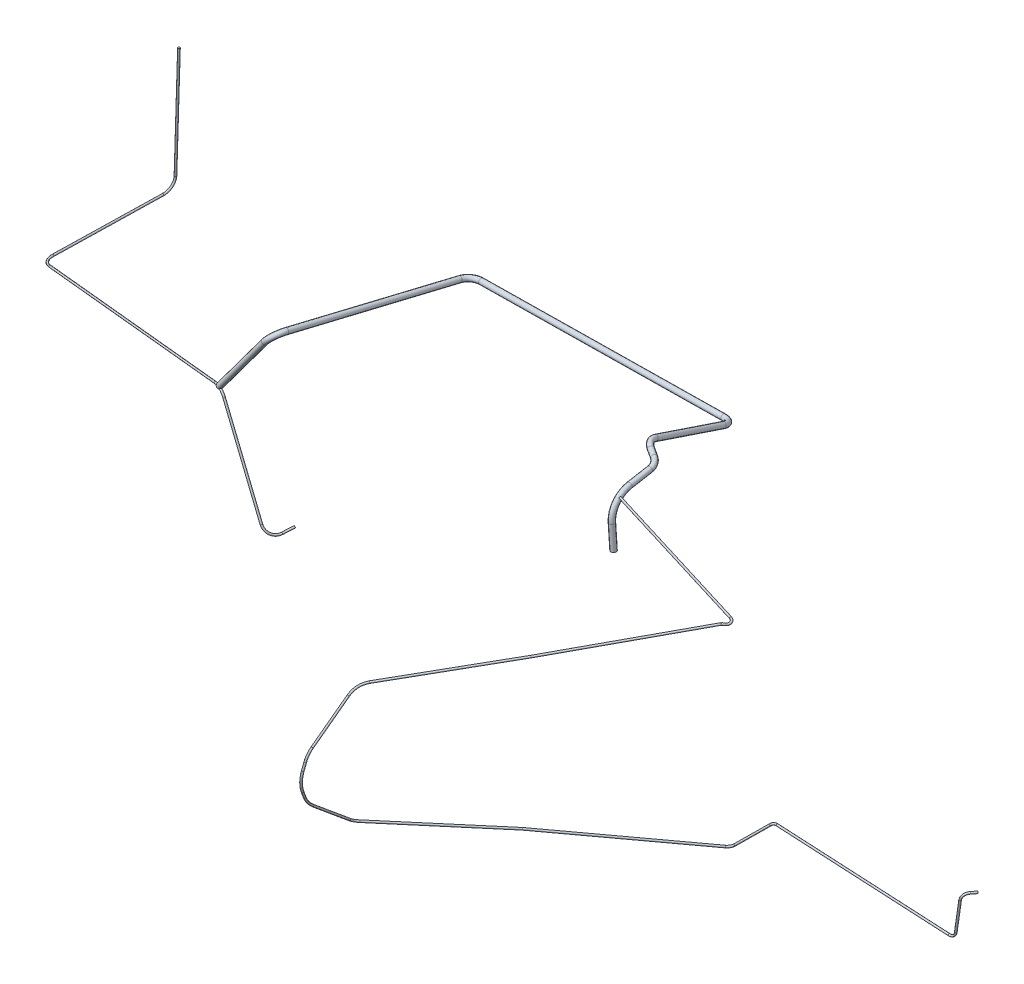
SolidWorks part; units mm, degrees
ref_plane "Front Plane" through (0, 0, 0) normal (0, 0, 1) x (1, 0, 0)
ref_plane "Top Plane" through (0, 0, 0) normal (0, 1, 0) x (1, 0, 0)
ref_plane "Right Plane" through (0, 0, 0) normal (1, 0, 0) x (0, 0, -1)
sketch3d "Szkic 3D1"
  line L0 (118.6334, -241.8152, 530.8128) -> (126.1477, -236.1929, 505.1914)
  line L1 (92.7074, -219.0471, 559.88) -> (-28.1616, -0.6474, 537.4445)
  line L2 (-58.5393, 14.2321, 530.3794) -> (-646.2538, -88.7961, 379.7568)
  line L3 (-668.6435, -91.6493, 348.0488) -> (-647.2132, -76.58, 79.4296)
  line L4 (-642.2695, -45.2392, 51.4403) -> (-614.8845, 270.4014, 69.5762)
  arc A0 (-642.2695, -45.2392, 51.4403) -> (-647.2132, -76.58, 79.4296) centre (-644.6374, -46.7499, 81.3085) ccw
  arc A1 (-668.6435, -91.6493, 348.0488) -> (-646.2538, -88.7961, 379.7568) centre (-639.2442, -86.2938, 350.6947) ccw
  arc A2 (-28.1616, -0.6474, 537.4445) -> (-58.5393, 14.2321, 530.3794) centre (-53.4158, -15.3263, 530.6067) ccw
  arc A3 (92.7074, -219.0471, 559.88) -> (118.6334, -241.8152, 530.8128) centre (102.9496, -216.2612, 531.8205) ccw
  spline S0 degree 3 poles (-43.8939, 18.1609, 559.9156) (-56.5359, -9.6744, 555.7329) (-50.4168, -8.8135, 531.5086) (-37.7748, 19.0219, 535.6913) knots 0 0 0 0 1 1 1 1 weights 1 0.333333 0.333333 1 construction
  point P0 (-614.8845, 270.4014, 69.5762)
  point P1 (-644.8442, -74.9142, 49.7352)
  point P3 (-670.6739, -93.077, 373.4983)
  point P5 (-38.3547, 17.7705, 535.5525)
  point P7 (109.21, -248.8658, 562.9432)
  point P10 (126.1477, -236.1929, 505.1914)
  point P19 (-644.8442, -74.9142, 49.7352)
  point P20 (-674.4316, -44.0371, 79.0837)
  point P23 (-670.6739, -93.077, 373.4983)
  point P24 (-644.7222, -56.8233, 351.911)
  point P27 (-38.3547, 17.7705, 535.5525)
  point P28 (-60.6885, -16.3632, 559.6933)
  point P31 (109.21, -248.8658, 562.9432)
  point P32 (127.1522, -201.8118, 542.0895)
  dimension "D1" = 30
  dimension "D2" = 30
  dimension "D3" = 30
  dimension "D4" = 30
sweep "Wyciągnięcie po ścieżce1" add path "Szkic 3D1" circular profile diameter 5 parameters "D3"=5
sketch3d "Szkic 3D3"
  line L0 (989.8027, 219.1816, 531.8369) -> (993.064, 156.0841, 530.7633)
  line L1 (987.1848, 269.8281, 532.6986) -> (993.064, 156.0841, 530.7633) construction
  line L2 (987.6129, 279.1527, 482.8435) -> (988.0685, 289.0787, 429.7731)
  line L3 (973.366, 297.4051, 404.5748) -> (955.7907, 303.4336, 395.2068)
  line L4 (938.0833, 303.0691, 365.1368) -> (941.6159, 246.4526, 189.4723)
  line L5 (913.4119, 235.9721, 160.7825) -> (245.1625, 197.8978, 131.614)
  line L6 (213.9993, 199.7803, 157.18) -> (154.871, 250.8882, 555.5945)
  line L7 (127.0667, 227.5957, 584.4501) -> (-45.7126, 13.3559, 531.0103)
  arc A0 (154.871, 250.8882, 555.5945) -> (127.0667, 227.5957, 584.4501) centre (135.1657, 228.2674, 555.5718) ccw
  arc A1 (245.1625, 197.8978, 131.614) -> (213.9993, 199.7803, 157.18) centre (243.6407, 201.8549, 161.3129) ccw
  arc A2 (941.6159, 246.4526, 189.4723) -> (913.4119, 235.9721, 160.7825) centre (911.6463, 245.1126, 189.3015) ccw
  arc A3 (938.0833, 303.0691, 365.1368) -> (955.7907, 303.4336, 395.2068) centre (965.0571, 290.7396, 369.653) ccw
  arc A4 (973.366, 297.4051, 404.5748) -> (988.0685, 289.0787, 429.7731) centre (958.8847, 295.9515, 430.8079) ccw
  arc A5 (987.6129, 279.1527, 482.8435) -> (989.8027, 219.1816, 531.8369) centre (990.8388, 220.2557, 471.8555) ccw
  point P0 (-45.7126, 13.3559, 531.0103)
  point P1 (149.5563, 255.482, 591.406)
  point P2 (217.9696, 196.3485, 130.427)
  point P3 (942.1676, 237.6104, 162.0377)
  point P4 (937.6728, 309.6481, 385.5497)
  point P5 (988.2169, 292.3112, 412.4905)
  point P6 (993.064, 156.0841, 530.7633)
  point P17 (149.5563, 255.482, 591.406)
  point P18 (157.3606, 208.9273, 561.3466)
  point P21 (217.9696, 196.3485, 130.427)
  point P22 (242.1252, 231.5438, 157.2795)
  point P25 (942.1676, 237.6104, 162.0377)
  point P26 (910.4235, 273.6353, 180.0841)
  point P29 (937.6728, 309.6481, 385.5497)
  point P30 (978.1752, 316.4947, 361.616)
  point P33 (988.2169, 292.3112, 412.4905)
  point P34 (951.9391, 267.2749, 425.3848)
  point P37 (987.1848, 269.8281, 532.6986)
  point P39 (1050.7499, 223.3339, 472.9456)
  point P40 (1025.4433, 280.7615, 422.3662)
  point P41 (0, 0, 0)
  point P42 (0, 0, 0)
  point P43 (1017.6285, 227.4395, 548.7936)
  point P44 (0, 0, 0)
  point P45 (996.948, 289.329, 478.9412)
  point P46 (996.9218, 289.3378, 480.9302)
  point P47 (0, 0, 0)
  point P48 (985.8788, 155.3262, 554.8039)
  point P49 (990.8026, 156.0347, 535.038)
  point P50 (0, 0, 0)
  point P51 (997.2337, 289.2337, 481.4121)
  point P52 (0, 0, 0)
  point P53 (996.4685, 282.7751, 481.4194)
  point P54 (991.2305, 283.0725, 481.6954)
  point P55 (987.6129, 279.1527, 482.8435)
  point P56 (0, 0, 0)
  point P57 (993.064, 156.0841, 530.7633)
  dimension "D1" = 30
  dimension "D2" = 30
  dimension "D3" = 30
  dimension "D4" = 30
  dimension "D5" = 30
  dimension "D6" = 60
sweep "Wyciągnięcie po ścieżce6" add path "Szkic 3D3" circular profile diameter 14 parameters "D3"=14
sketch3d "Szkic 3D5"
  line L5 (1297.1378, 181.2424, 546.2056) -> (993.3621, 268.815, 513.8045)
  point P0 (993.3621, 268.815, 513.8045)
  point P1 (0, 0, 0)
  point P2 (0, 0, 0)
  point P3 (0, 0, 0)
  point P4 (1297.1378, 181.2424, 546.2056)
sweep "Wyciągnięcie po ścieżce8" add path "Szkic 3D5" circular profile diameter 5 parameters "D3"=5
sketch3d "Szkic 3D7"
  line L0 (1317.9997, 171.2228, 571.7296) -> (1089.6413, 119.1433, 845.116)
  line L1 (1089.6413, 119.1433, 845.116) -> (892.0087, 75.9961, 1072.9769)
  line L2 (873.0448, 54.6235, 1110.3704) -> (862.0854, -27.3683, 1194.7376)
  line L3 (859.4121, -54.1309, 1210.6137) -> (858.0564, -72.0891, 1215.615)
  line L4 (854.0483, -123.8873, 1212.4709) -> (852.7489, -140.2636, 1205.6842)
  line L5 (851.4146, -171.5957, 1182.5394) -> (852.2453, -250.6918, 1087.0711)
  line L6 (859.9208, -260.558, 1067.5275) -> (1046.5433, -305.8392, 825.1721)
  arc A0 (873.0448, 54.6235, 1110.3704) -> (892.0087, 75.9961, 1072.9769) centre (921.6424, 26.4429, 1089.2961) ccw
  arc A1 (859.4121, -54.1309, 1210.6137) -> (862.0854, -27.3683, 1194.7376) centre (862.9992, -70.4504, 1152.9872) ccw
  arc A2 (854.0483, -123.8873, 1212.4709) -> (858.0564, -72.0891, 1215.615) centre (855.986, -93.3997, 1138.5334) ccw
  arc A3 (851.4146, -171.5957, 1182.5394) -> (852.7489, -140.2636, 1205.6842) centre (864.7911, -110.8021, 1132.288) ccw
  arc A4 (859.9208, -260.558, 1067.5275) -> (852.2453, -250.6918, 1087.0711) centre (877.4361, -238.0392, 1076.8075) ccw
  point P1 (875.4174, 72.3739, 1092.1058)
  point P2 (860.5852, -38.5915, 1206.286)
  point P3 (856.0602, -98.5312, 1222.979)
  point P4 (851.28, -158.7766, 1198.012)
  point P5 (852.3296, -258.7161, 1077.3857)
  point P6 (1046.5433, -305.8392, 825.1721)
  point P7 (1089.6413, 119.1433, 845.116)
  point P8 (1317.9997, 171.2228, 571.7296)
  point P9 (1317.9997, 171.2228, 571.7296)
  point P10 (1089.6413, 119.1433, 845.116)
  point P11 (1317.9997, 171.2228, 571.7296)
  point P20 (1344.5343, 169.194, 550.9786)
  point P22 (875.4174, 72.3739, 1092.1058)
  point P23 (886.8962, -6.3029, 1052.9587)
  point P26 (860.5852, -38.5915, 1206.286)
  point P27 (803.2649, -67.2304, 1148.357)
  point P30 (856.0602, -98.5312, 1222.979)
  point P31 (776.2236, -87.2547, 1138.9768)
  point P34 (851.28, -158.7766, 1198.012)
  point P35 (785.9191, -100.8386, 1123.3468)
  point P38 (852.3296, -258.7161, 1077.3857)
  point P39 (861.1454, -218.7104, 1060.6517)
  point P40 (1344.8319, 167.7288, 549.6777)
  point P41 (1346.3485, 167.7529, 549.2822)
  point P42 (0, 0, 0)
  point P43 (0, 0, 0)
  point P44 (928.6967, 42.8842, 509.4356)
  point P45 (1026.5062, 427.7046, 632.5039)
  point P46 (0, 0, 0)
  point P47 (1015.5264, 364.4728, 564.5444)
  point P48 (950.6862, 112.5248, 491.4952)
  point P49 (841.9268, -160.1525, 774.184)
  point P50 (1171.444, 37.1322, 483.201)
  point P51 (1233.7113, 209.6921, 505.3444)
  point P52 (0, 0, 0)
  point P53 (1304.541, 240.922, 556.3461)
  point P54 (1299.8089, 183.2482, 535.0836)
  point P55 (1329.2568, 167.4699, 554.1711)
  point P56 (1317.9997, 171.2228, 571.7296)
  dimension "D1" = 60
  dimension "D2" = 60
  dimension "D3" = 80
  dimension "D4" = 80
  dimension "D5" = 30
  dimension "D6" = 360
sweep "Wyciągnięcie po ścieżce9" add path "Szkic 3D7" circular profile diameter 5 parameters "D3"=5
sketch3d "3DSketch3"
  line L0 (1297.1378, 181.2424, 546.2056) -> (1319.4526, 174.8095, 548.5857)
  line L1 (1324.5208, 170.5494, 565.4072) -> (1317.9997, 171.2228, 571.7296)
  arc A0 (1324.5208, 170.5494, 565.4072) -> (1319.4526, 174.8095, 548.5857) centre (1318.0304, 173.5065, 558.3979) ccw
  point P3 (1297.1378, 181.2424, 546.2056)
  point P4 (0, 0, 0)
  point P5 (0, 0, 0)
  point P6 (1317.9997, 171.2228, 571.7296)
  point P7 (0, 0, 0)
  point P8 (1329.7497, 178.9952, 551.6018)
  point P10 (1339.6491, 168.9873, 550.7399)
  point P11 (1317.9997, 171.2228, 571.7296)
  point P12 (0, 0, 0)
  point P13 (0, 0, 0)
  point P15 (1339.6491, 168.9873, 550.7399)
  point P16 (1320.6014, 183.0306, 560.0353)
  dimension "D1" = 10
sweep "Sweep2" add path "3DSketch3" circular profile diameter 5 parameters "D3"=5
sketch3d "3DSketch4"
  line L0 (1046.5433, -305.8392, 825.1721) -> (1289.7034, -370.8587, 533.1913)
  line L1 (1304.1193, -365.3423, 521.6908) -> (1370.2112, -300.3311, 493.5914)
  line L2 (1385.1466, -294.2844, 491.5366) -> (1867.7121, -289.8097, 519.9949)
  line L3 (1887.1006, -273.5725, 521.7897) -> (1902.7775, -190.3056, 526.0857)
  line L4 (1917.6489, -172.2827, 513.9402) -> (1927.0499, -171.593, 503.4145)
  arc A0 (1289.7034, -370.8587, 533.1913) -> (1304.1193, -365.3423, 521.6908) centre (1297.8493, -352.803, 535.9544) ccw
  arc A1 (1917.6489, -172.2827, 513.9402) -> (1902.7775, -190.3056, 526.0857) centre (1915.7074, -191.9574, 510.917) ccw
  arc A2 (1867.7121, -289.8097, 519.9949) -> (1887.1006, -273.5725, 521.7897) centre (1867.4798, -269.8269, 520.7919) ccw
  arc A3 (1385.1466, -294.2844, 491.5366) -> (1370.2112, -300.3311, 493.5914) centre (1384.7891, -312.2015, 500.4162) ccw
  point P0 (1046.5433, -305.8392, 825.1721)
  point P1 (1296.6287, -372.7105, 524.8755)
  point P2 (1376.2748, -294.3666, 491.0134)
  point P3 (1884.0721, -289.658, 520.9597)
  point P4 (1903.0121, -194.6767, 526.1838)
  point P5 (1906.01, -173.1366, 526.9715)
  point P6 (1927.0499, -171.593, 503.4145)
  point P15 (1296.6287, -372.7105, 524.8755)
  point P16 (1311.0589, -360.7157, 548.7174)
  point P19 (1906.01, -173.1366, 526.9715)
  point P20 (1930.5115, -195.4151, 523.9126)
  point P23 (1884.0721, -289.658, 520.9597)
  point P24 (1866.3108, -270.6361, 540.7413)
  point P27 (1376.2748, -294.3666, 491.0134)
  point P28 (1383.6522, -303.3166, 518.2982)
  dimension "D1" = 20
  dimension "D2" = 20
sweep "Sweep3" add path "3DSketch4" circular profile diameter 5 parameters "D3"=5
